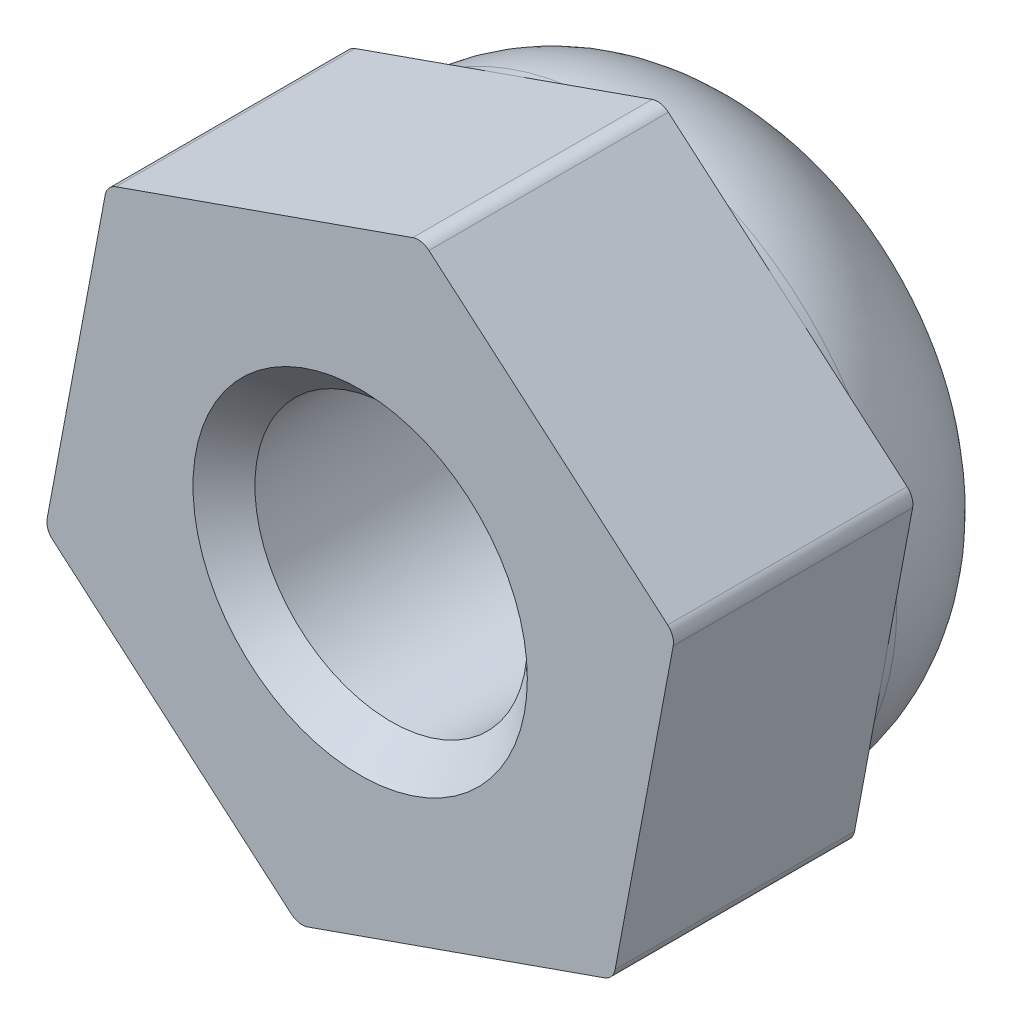
SolidWorks part; units mm, degrees
ref_plane "前视基准面" through (0, 0, 0) normal (0, 0, 1) x (1, 0, 0)
ref_plane "上视基准面" through (0, 0, 0) normal (0, 1, 0) x (1, 0, 0)
ref_plane "右视基准面" through (0, 0, 0) normal (1, 0, 0) x (0, 0, -1)
sketch "草图1" plane through (0, 0, 0) normal (0, 0, 1) x (1, 0, 0)
  line L1 (3.0672, -2.6317) -> (3.8127, 1.3404)
  line L2 (3.8127, 1.3404) -> (0.7455, 3.9721)
  line L3 (0.7455, 3.9721) -> (-3.0672, 2.6317)
  line L4 (-3.0672, 2.6317) -> (-3.8127, -1.3404)
  line L5 (-3.8127, -1.3404) -> (-0.7455, -3.9721)
  line L6 (-0.7455, -3.9721) -> (3.0672, -2.6317)
  circle A0 centre (0, 0) radius 3.5 construction
  dimension "D1" = 7
extrude "凸台-拉伸1" add sketch "草图1" along normal blind 2.9
sketch "草图2" plane through (0, 0, 2.9) normal (0, 0, 1) x (1, 0, 0)
  line L0 (3.8127, 1.3404) -> (0.7455, 3.9721) construction
  circle A0 centre (0, 0) radius 3.5
extrude "凸台-拉伸3" add sketch "草图2" against normal blind 5
fillet "圆角1" radius 2 1 edges at (3.5, 0, -2.1)
fillet "圆角2" radius 0.2 6 edges at (3.0672, -2.6317, 1.45) (3.8127, 1.3404, 1.45) (0.7455, 3.9721, 1.45) (-3.0672, 2.6317, 1.45) (-3.8127, -1.3404, 1.45) (-0.7455, -3.9721, 1.45)
hole_wizard "M4 螺纹孔2" positions "草图8" profile "草图7" tap size "M4" standard "GB"
sketch "草图8" plane through (0, 0, 2.9) normal (0, 0, 1) x (1, 0, 0)
  point P0 (0, 0)
sketch "草图7" plane through (0, 0, 2.9) normal (1, 0, 0) x (0, -1, 0)
  line L0 (0, 0) -> (0, 11.0914)
  line L1 (0, 11.0914) -> (1.65, 10.1)
  line L2 (1.65, 10.1) -> (1.65, 0.375)
  line L3 (1.65, 0.375) -> (2.025, 0)
  line L5 (2.025, 0) -> (0, 0)
  line L6 (-1.65, 0.375) -> (-2.025, 0) construction
  line L10 (0, 11.0914) -> (-1.65, 10.1) construction
  line L11 (0, -6.35) -> (0, 107.95) construction
  dimension "螺纹孔钻头直径" = 3.3
  dimension "螺纹孔钻头深度" = 10.1
  dimension "近端锥形沉头孔直径" = 4.05
  dimension "近端锥形沉头孔角度" = 90
  dimension "导头角度" = 118
cosmetic thread "孔螺蚊线2" parameters "D1"=4.9944, "D2"=4
